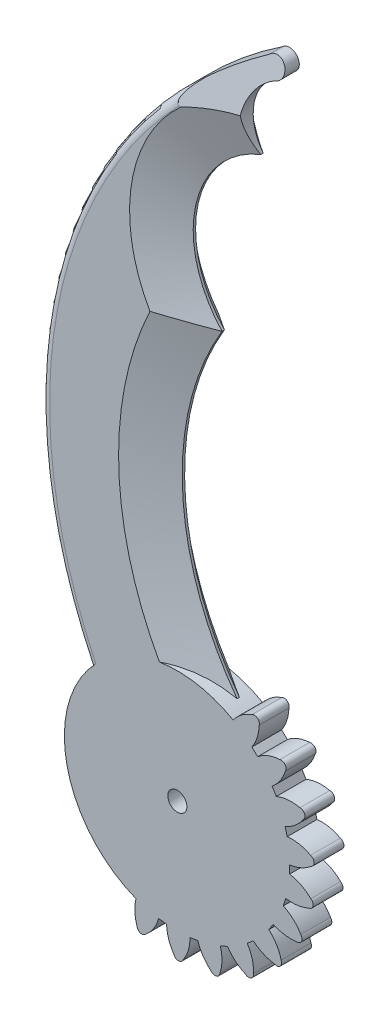
SolidWorks part; units mm, degrees
ref_plane "Alzado" through (0, 0, 0) normal (0, 0, 1) x (1, 0, 0)
ref_plane "Planta" through (0, 0, 0) normal (0, 1, 0) x (1, 0, 0)
ref_plane "Vista lateral" through (0, 0, 0) normal (1, 0, 0) x (0, 0, -1)
sketch "Croquis1" plane through (0, 0, 0) normal (0, 0, 1) x (1, 0, 0)
  line L17 (-3.2126, -18.6557) -> (-1.8838, -18.8189)
  line L20 (-0.0726, -0.0418) -> (19.5255, 27.0183) construction
  line L21 (-0.0726, -0.0418) -> (-11.3011, -25.1705) construction
  line L22 (2.0397, -18.8002) -> (3.3621, -18.5908)
  line L23 (7.1284, -17.4913) -> (8.3418, -16.9255)
  line L24 (11.6592, -14.8305) -> (12.6696, -13.9521)
  line L25 (15.281, -11.0239) -> (16.0102, -9.901)
  line L26 (17.7133, -6.3664) -> (18.1048, -5.0861)
  line L27 (18.7676, -1.219) -> (18.791, 0.1197)
  line L28 (18.3623, 4.0197) -> (18.0157, 5.3129)
  line L29 (16.5286, 8.9437) -> (15.8391, 10.0913)
  line L30 (13.4088, 13.1715) -> (12.4296, 14.0846)
  arc A42 (-14.8246, 11.8737) -> (12.5832, 113.4585) centre (56.7102, 47.0633) cw
  arc A43 (14.1918, 110.7057) -> (12.5832, 113.4585) centre (13.7491, 112.2934) ccw
  arc A44 (14.1918, 110.7057) -> (11.4368, 98.4517) centre (17.9357, 103.4273) ccw
  arc A45 (11.4368, 98.4517) -> (4.9305, 69.5123) centre (18.0189, 81.7708) ccw
  arc A46 (4.9305, 69.5123) -> (7.4484, 17.3661) centre (45.3244, 45.3288) ccw
  circle A48 centre (-0.0726, -0.0418) radius 1.6
  arc A49 (-0.6568, -22.5875) -> (-1.8838, -18.8189) centre (5.174, -18.6049) cw
  arc A50 (-0.6568, -22.5875) -> (0.882, -22.6231) centre (0.1191, -22.3237) ccw
  arc A51 (2.0397, -18.8002) -> (0.882, -22.6231) centre (-4.3966, -18.9378) cw
  arc A52 (-6.8486, -21.5531) -> (-7.0132, -17.6891) centre (-0.1459, -19.332) cw
  arc A53 (-6.8486, -21.5531) -> (-5.3792, -22.0114) centre (-6.03, -21.5134) ccw
  arc A54 (-3.2126, -18.6557) -> (-5.3792, -22.0114) centre (-9.4375, -17.0139) cw
  arc A55 (5.5803, -21.8751) -> (3.3621, -18.5908) centre (10.0875, -16.4397) cw
  arc A56 (5.5803, -21.8751) -> (7.0692, -21.4852) centre (6.2534, -21.4077) ccw
  arc A57 (7.1284, -17.4913) -> (7.0692, -21.4852) centre (0.9794, -19.3976) cw
  arc A58 (11.3794, -19.4712) -> (8.3418, -16.9255) centre (14.2138, -13.0039) cw
  arc A59 (11.3794, -19.4712) -> (12.7032, -18.686) centre (11.8976, -18.8363) ccw
  arc A60 (11.6592, -14.8305) -> (12.7032, -18.686) centre (6.2738, -18.3578) cw
  arc A61 (16.2912, -15.5619) -> (12.6696, -13.9521) centre (17.2332, -8.564) cw
  arc A62 (16.2912, -15.5619) -> (17.3473, -14.4422) centre (16.6144, -14.8088) ccw
  arc A63 (15.281, -11.0239) -> (17.3473, -14.4422) centre (11.0765, -15.899) cw
  arc A64 (19.9352, -10.4502) -> (16.0102, -9.901) centre (18.9118, -3.4637) cw
  arc A65 (19.9352, -10.4502) -> (20.6418, -9.0828) centre (20.0383, -9.6372) ccw
  arc A66 (17.7133, -6.3664) -> (20.6418, -9.0828) centre (15.0155, -12.2116) cw
  arc A67 (22.0291, -4.5321) -> (18.1048, -5.0861) centre (19.1196, 1.9017) cw
  arc A68 (22.0291, -4.5321) -> (22.3314, -3.0229) centre (21.9041, -3.7222) ccw
  arc A69 (18.7676, -1.219) -> (22.3314, -3.0229) centre (17.7855, -7.5813) cw
  arc A70 (22.4106, 1.7339) -> (18.791, 0.1197) centre (17.8404, 7.1165) cw
  arc A71 (22.4106, 1.7339) -> (22.2852, 3.2679) centre (22.0672, 2.478) ccw
  arc A72 (18.3623, 4.0197) -> (22.2852, 3.2679) centre (19.1718, -2.3669) cw
  arc A73 (21.0502, 7.8623) -> (18.0157, 5.3129) centre (15.1734, 11.7767) cw
  arc A74 (21.0502, 7.8623) -> (20.5068, 9.3024) centre (20.515, 8.4829) ccw
  arc A75 (16.5286, 8.9437) -> (20.5068, 9.3024) centre (19.0672, 3.0276) cw
  arc A76 (18.0533, 13.3784) -> (15.8391, 10.0913) centre (11.3252, 15.5212) cw
  arc A77 (18.0533, 13.3784) -> (17.134, 14.6128) centre (17.3678, 13.8274) ccw
  arc A78 (13.4088, 13.1715) -> (17.134, 14.6128) centre (17.4797, 8.1844) cw
  arc A79 (13.652, 17.8547) -> (12.4296, 14.0846) centre (6.594, 18.06) cw
  arc A80 (13.652, 17.8547) -> (12.4281, 18.7879) centre (12.8693, 18.0973) ccw
  arc A81 (9.2943, 16.4464) -> (12.4281, 18.7879) centre (14.5324, 12.7038) cw
  arc A82 (9.2943, 16.4464) -> (7.4484, 17.3661) centre (-0.0726, -0.0418) ccw
  arc A83 (-14.8246, 11.8737) -> (-7.0132, -17.6891) centre (-0.0726, -0.0418) ccw
  point P120 (-0.0726, -0.0418)
  point P201 (-0.0726, -0.0418)
extrude "Base pinza Izq" add sketch "Croquis1" along normal blind 5
chamfer "Filo Pinza Izq frente" distance 2.5 angle 73 2 edges at (0.5231, 85.7043, 5) (-1.7006, 43.0582, 5)
chamfer "Filo Pinza Izq trasera" distance 2.5 angle 40 3 edges at (9.9502, 105.2226, 0) (-1.7006, 43.0582, 0) (0.5231, 85.7043, 0)
fillet "Redondeo pinza" radius 1.5 1 edges at (-20.2591, 67.8297, 5)
sketch "Croquis2" plane through (0, 0, 0) normal (1, 0, 0) x (0, 0, -1)
  line L4 (-5, 101.1693) -> (-1.113, 118.0938)
  line L5 (-5, 106.7628) -> (-5, 68.8565) construction
  line L6 (-1.113, 118.0938) -> (-5, 118.0938)
  line L7 (-5, 118.0938) -> (-5, 101.1693)
extrude "Filo punta de la pinza" cut sketch "Croquis2" along normal blind 25
